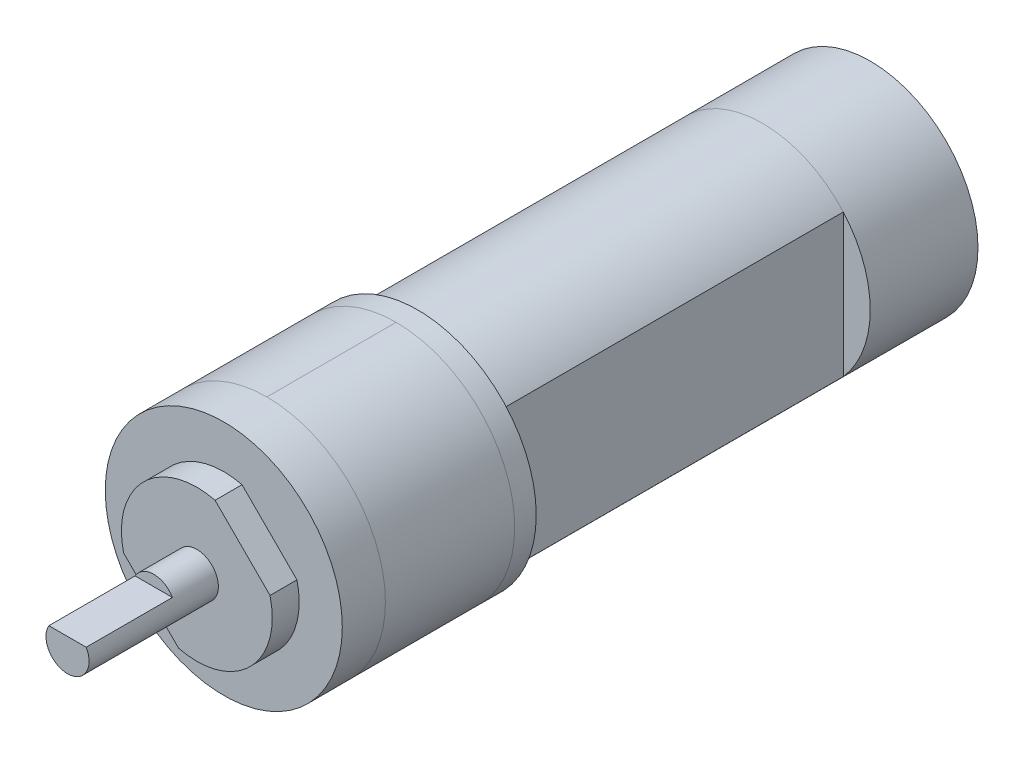
SolidWorks part; units mm, degrees
ref_plane "Front Plane" through (0, 0, 0) normal (0, 0, 1) x (1, 0, 0)
ref_plane "Top Plane" through (0, 0, 0) normal (0, 1, 0) x (1, 0, 0)
ref_plane "Right Plane" through (0, 0, 0) normal (1, 0, 0) x (0, 0, -1)
sketch "Sketch2" plane through (0, 0, 0) normal (1, 0, 0) x (0, 0, -1)
  line L0 (0, 0) -> (0, 11)
  line L1 (0, 11) -> (-18, 11)
  line L2 (-18, 11) -> (-18, 0)
  line L3 (-18, 7) -> (-20.5, 7)
  line L4 (-20.5, 7) -> (-20.5, 0)
  line L5 (-51.2955, 0) -> (51.2955, 0) construction
  line L6 (0, 10) -> (32, 10)
  line L7 (32, 10) -> (32, 0)
  line L8 (32, 10) -> (42, 10)
  line L9 (42, 10) -> (42, 0)
  point P11 (0, 0)
  dimension "D1" = 14
  dimension "D2" = 22
  dimension "D3" = 2.5
  dimension "D4" = 18
  dimension "D5" = 32
  dimension "D6" = 20
  dimension "D7" = 10
revolve "Revolve1" add sketch "Sketch2" angle 360 about L5
sketch "Sketch4" plane through (0, 0, 0) normal (0, 0, -1) x (-1, 0, 0)
  line L1 (-7.5, -11) -> (7.5, -11) construction
  line L2 (-7.5, -11) -> (-7.5, 11) construction
  line L3 (-7.5, 11) -> (7.5, 11) construction
  line L4 (7.5, -11) -> (7.5, 11) construction
  line L5 (-7.5, -11) -> (7.5, 11) construction
  line L6 (-7.5, 11) -> (7.5, -11) construction
  line L7 (-7.5, 11) -> (-11, 11)
  line L8 (-7.5, 11) -> (-7.5, -11)
  line L9 (-7.5, -11) -> (-11, -11)
  line L10 (-11, 11) -> (-11, -11)
  line L11 (7.5, 11) -> (11, 11)
  line L12 (7.5, 11) -> (7.5, -11)
  line L13 (7.5, -11) -> (11, -11)
  line L14 (11, 11) -> (11, -11)
  circle A0 centre (0, 0) radius 11 construction
  point P0 (0, 0)
  dimension "D1" = 15
extrude "Cut-Extrude1" cut sketch "Sketch4" along normal offset from surface (32 mm away) 10 up to face at (10, 0, -42)
sketch "Sketch5" plane through (0, 0, 20.5) normal (0, 0, 1) x (1, 0, 0)
  line L0 (-4.9497, 4.9497) -> (4.9497, -4.9497) construction
  line L1 (0, 0) -> (0, 7) construction
  line L2 (-9.1924, 0.7071) -> (0.7071, -9.1924)
  line L3 (-0.7071, 9.1924) -> (9.1924, -0.7071)
  line L4 (-0.7071, 9.1924) -> (2.8284, 12.7279)
  line L5 (2.8284, 12.7279) -> (12.7279, 2.8284)
  line L6 (12.7279, 2.8284) -> (9.1924, -0.7071)
  line L7 (-9.1924, 0.7071) -> (-12.7279, -2.8284)
  line L8 (-12.7279, -2.8284) -> (-2.8284, -12.7279)
  line L9 (-2.8284, -12.7279) -> (0.7071, -9.1924)
  circle A0 centre (0, 0) radius 7 construction
  circle A1 centre (0, 0) radius 7 construction
  circle A2 centre (0, 0) radius 11 construction
  point P6 (0, 0)
  dimension "D1" = 45
  dimension "D2" = 6
  dimension "D3" = 6
extrude "Cut-Extrude2" cut sketch "Sketch5" against normal up to surface (2.5 mm away) up to face at (7, 0, 18)
sketch "Sketch6" plane through (0, 0, 20.5) normal (0, 0, 1) x (1, 0, 0)
  circle A0 centre (0, 0) radius 2
  dimension "D1" = 4
extrude "Boss-Extrude1" add sketch "Sketch6" along normal blind 12
sketch "Sketch7" plane through (0, 0, 32.5) normal (0, 0, 1) x (1, 0, 0)
  line L1 (-2, 1) -> (2, 1)
  line L2 (-2, 1) -> (-2, 3)
  line L3 (-2, 3) -> (2, 3)
  line L4 (2, 1) -> (2, 3)
  line L5 (-2, 1) -> (2, 3) construction
  line L6 (-2, 3) -> (2, 1) construction
  circle A0 centre (0, 0) radius 2 construction
  circle A1 centre (0, 0) radius 2 construction
  point P0 (0, 2)
  dimension "D1" = 3
extrude "Cut-Extrude3" cut sketch "Sketch7" against normal blind 8
sketch "Sketch8" plane through (0, 0, 0) normal (1, 0, 0) x (0, 0, -1)
  line L0 (0, 11) -> (-18, 11) construction
  line L1 (-14, 11) -> (-2, 11)
  line L2 (-14, 11) -> (-14, -11)
  line L3 (-14, -11) -> (-2, -11)
  line L4 (-2, 11) -> (-2, -11)
  line L5 (-18, -11) -> (0, -11) construction
  line L6 (32, 10) -> (32, -10)
  line L7 (42, 10) -> (0, 10) construction
  line L8 (0, -10) -> (42, -10) construction
  line L9 (32, -6.6144) -> (32, 6.6144) construction
  line L10 (-18, 11) -> (-18, -11) construction
  line L11 (0, -6.6144) -> (0, 6.6144) construction
  dimension "D1" = 4
  dimension "D2" = 2
split line "Split Line1"
